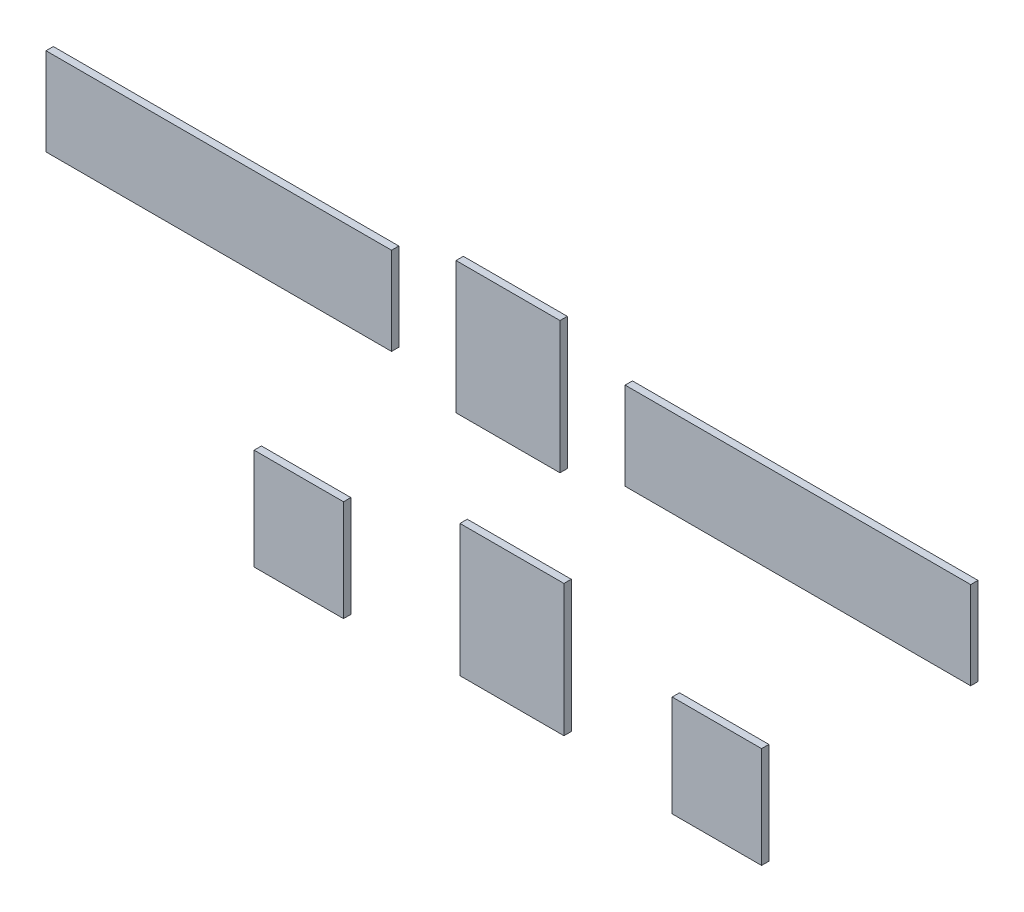
SolidWorks part; units mm, degrees
ref_plane "Front Plane" through (0, 0, 0) normal (0, 0, 1) x (1, 0, 0)
ref_plane "Top Plane" through (0, 0, 0) normal (0, 1, 0) x (1, 0, 0)
ref_plane "Right Plane" through (0, 0, 0) normal (1, 0, 0) x (0, 0, -1)
sketch "Sketch1" plane through (0, 0, 0) normal (0, 0, 1) x (1, 0, 0)
  line L0 (-95.4432, -29.7782) -> (-395.4432, -29.7782)
  line L1 (407.3568, -29.7782) -> (107.3568, -29.7782)
  line L2 (407.3568, -29.7782) -> (407.3568, 46.3301)
  line L3 (407.3568, 46.3301) -> (107.3568, 46.3301)
  line L4 (107.3568, -29.7782) -> (107.3568, 46.3301)
  line L5 (-95.4432, -29.7782) -> (-95.4432, 46.3301)
  line L6 (-95.4432, 46.3301) -> (-395.4432, 46.3301)
  line L7 (-395.4432, -29.7782) -> (-395.4432, 46.3301)
  line L8 (412.3568, 76.4806) -> (412.3568, -56.8694) construction
  line L10 (-226.1738, 3.4556) -> (-226.1738, -9.2444) construction
  line L11 (54.2281, -243.8934) -> (-36.0278, -243.8934)
  line L12 (50.776, -47.935) -> (-39.4799, -47.935)
  line L13 (50.776, -47.935) -> (50.776, 66.5878)
  line L14 (50.776, 66.5878) -> (-39.4799, 66.5878)
  line L15 (-39.4799, -47.935) -> (-39.4799, 66.5878)
  line L16 (54.2281, -243.8934) -> (54.2281, -129.3706)
  line L17 (54.2281, -129.3706) -> (-36.0278, -129.3706)
  line L18 (-36.0278, -243.8934) -> (-36.0278, -129.3706)
  line L19 (-137.15, -251.5314) -> (-214.7482, -251.5314)
  line L20 (-137.15, -251.5314) -> (-137.15, -163.6452)
  line L21 (-137.15, -163.6452) -> (-214.7482, -163.6452)
  line L22 (-214.7482, -251.5314) -> (-214.7482, -163.6452)
  line L23 (225.8162, -255.6443) -> (148.218, -255.6443)
  line L24 (225.8162, -255.6443) -> (225.8162, -167.7581)
  line L25 (225.8162, -167.7581) -> (148.218, -167.7581)
  line L26 (148.218, -255.6443) -> (148.218, -167.7581)
  point P26 (-501.3453, 73.0257)
  dimension "D1" = 0
  dimension "D2" = 5
  dimension "D4" = 169.2694
  dimension "D6" = 300
extrude "Boss-Extrude1" add sketch "Sketch1" along normal blind 6.35
